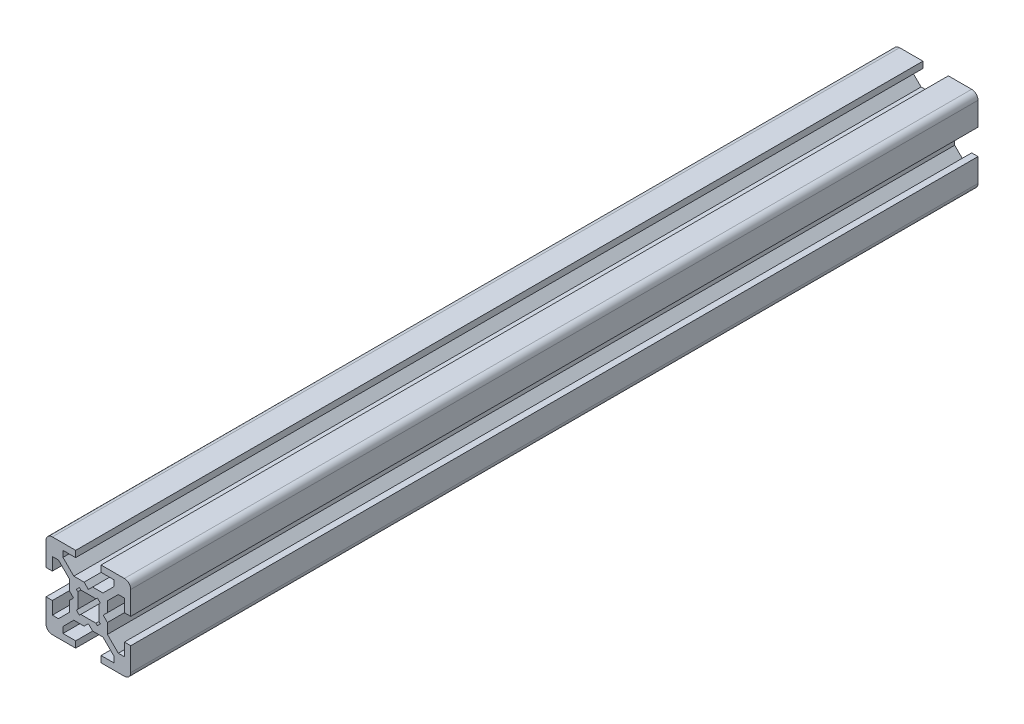
SolidWorks part; units mm, degrees
ref_plane "Front Plane" through (0, 0, 0) normal (0, 0, 1) x (1, 0, 0)
ref_plane "Top Plane" through (0, 0, 0) normal (0, 1, 0) x (1, 0, 0)
ref_plane "Right Plane" through (0, 0, 0) normal (1, 0, 0) x (0, 0, -1)
sketch "Sketch1" plane through (0, 0, 0) normal (0, 0, 1) x (1, 0, 0)
  line L0 (0, -1000) -> (0, 49000) construction
  line L1 (-1000, 0) -> (49000, 0) construction
  line L2 (0, 3.5) -> (1, 4.5)
  line L3 (1, 4.5) -> (3.4393, 4.5)
  line L4 (3.4393, 4.5) -> (6, 7.0607)
  line L5 (6, 7.0607) -> (6, 8.5)
  line L6 (6, 8.5) -> (3, 8.5)
  line L7 (3, 8.5) -> (3, 10)
  line L8 (3, 10) -> (10, 10)
  line L9 (0, 0) -> (35355.3391, 35355.3391) construction
  line L10 (-1.7929, 2.5) -> (1.7929, 2.5)
  line L11 (1.7929, 2.5) -> (2.1213, 2.8284)
  line L12 (2.1213, 2.8284) -> (2.8284, 2.1213)
  line L13 (2.5, 1.7929) -> (2.8284, 2.1213)
  line L14 (2.5, -1.7929) -> (2.5, 1.7929)
  line L15 (3.5, 0) -> (4.5, 1)
  line L16 (4.5, 1) -> (4.5, 3.4393)
  line L17 (4.5, 3.4393) -> (7.0607, 6)
  line L18 (7.0607, 6) -> (8.5, 6)
  line L19 (8.5, 6) -> (8.5, 3)
  line L20 (8.5, 3) -> (10, 3)
  line L21 (10, 3) -> (10, 10)
  line L22 (-3.5, 0) -> (-4.5, 1)
  line L23 (-2.5, -1.7929) -> (-2.5, 1.7929)
  line L24 (0, 3.5) -> (-1, 4.5)
  line L25 (-10, 3) -> (-10, 10)
  line L26 (-8.5, 3) -> (-10, 3)
  line L27 (-8.5, 6) -> (-8.5, 3)
  line L28 (-7.0607, 6) -> (-8.5, 6)
  line L29 (-4.5, 3.4393) -> (-7.0607, 6)
  line L30 (-4.5, 1) -> (-4.5, 3.4393)
  line L31 (-2.5, 1.7929) -> (-2.8284, 2.1213)
  line L32 (-2.1213, 2.8284) -> (-2.8284, 2.1213)
  line L33 (-1.7929, 2.5) -> (-2.1213, 2.8284)
  line L34 (-3, 10) -> (-10, 10)
  line L35 (-3, 8.5) -> (-3, 10)
  line L36 (-6, 8.5) -> (-3, 8.5)
  line L37 (-6, 7.0607) -> (-6, 8.5)
  line L38 (-3.4393, 4.5) -> (-6, 7.0607)
  line L39 (-1, 4.5) -> (-3.4393, 4.5)
  line L40 (8.5, -3) -> (10, -3)
  line L41 (8.5, -6) -> (8.5, -3)
  line L42 (7.0607, -6) -> (8.5, -6)
  line L43 (10, -3) -> (10, -10)
  line L44 (3, -10) -> (10, -10)
  line L45 (3, -8.5) -> (3, -10)
  line L46 (-3, -8.5) -> (-3, -10)
  line L47 (6, -8.5) -> (3, -8.5)
  line L48 (6, -7.0607) -> (6, -8.5)
  line L49 (3.4393, -4.5) -> (6, -7.0607)
  line L50 (4.5, -3.4393) -> (7.0607, -6)
  line L51 (4.5, -1) -> (4.5, -3.4393)
  line L52 (3.5, 0) -> (4.5, -1)
  line L53 (2.5, -1.7929) -> (2.8284, -2.1213)
  line L54 (2.1213, -2.8284) -> (2.8284, -2.1213)
  line L55 (1.7929, -2.5) -> (2.1213, -2.8284)
  line L56 (1, -4.5) -> (3.4393, -4.5)
  line L57 (0, -3.5) -> (1, -4.5)
  line L58 (-1, -4.5) -> (-3.4393, -4.5)
  line L59 (-3.4393, -4.5) -> (-6, -7.0607)
  line L60 (-6, -7.0607) -> (-6, -8.5)
  line L61 (-6, -8.5) -> (-3, -8.5)
  line L62 (-3, -10) -> (-10, -10)
  line L63 (-10, -3) -> (-10, -10)
  line L64 (-8.5, -3) -> (-10, -3)
  line L65 (-8.5, -6) -> (-8.5, -3)
  line L66 (-7.0607, -6) -> (-8.5, -6)
  line L67 (-4.5, -3.4393) -> (-7.0607, -6)
  line L68 (-4.5, -1) -> (-4.5, -3.4393)
  line L69 (-3.5, 0) -> (-4.5, -1)
  line L70 (-2.5, -1.7929) -> (-2.8284, -2.1213)
  line L71 (-2.1213, -2.8284) -> (-2.8284, -2.1213)
  line L72 (-1.7929, -2.5) -> (-2.1213, -2.8284)
  line L73 (-1.7929, -2.5) -> (1.7929, -2.5)
  line L74 (0, -3.5) -> (-1, -4.5)
  point P18 (2.4749, 2.4749)
  point P19 (4.5, 8.5)
  point P35 (0, 2.5)
  point P64 (2.5, 0)
  point P81 (-2.5, 0)
  dimension "D2" = 20
  dimension "D3" = 7
  dimension "D4" = 1.5
  dimension "D5" = 1.5
  dimension "D6" = 4
  dimension "D7" = 1
  dimension "D8" = 9
  dimension "D9" = 5
  dimension "D10" = 1
  dimension "D11" = 3.5
extrude "Boss-Extrude1" add sketch "Sketch1" along normal blind 200
fillet "Fillet1" radius 1.5 4 edges at (-10, -10, 100) (10, -10, 100) (10, 10, 100) (-10, 10, 100)
